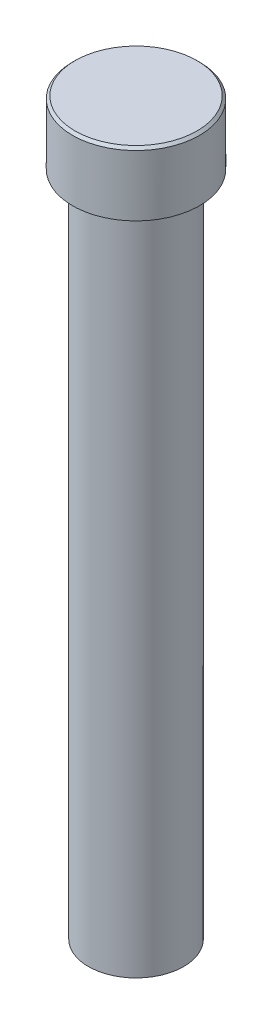
SolidWorks part; units mm, degrees
ref_plane "Front Plane" through (0, 0, 0) normal (0, 0, 1) x (1, 0, 0)
ref_plane "Top Plane" through (0, 0, 0) normal (0, 1, 0) x (1, 0, 0)
ref_plane "Right Plane" through (0, 0, 0) normal (1, 0, 0) x (0, 0, -1)
sketch "Sketch2" plane through (0, 0, 0) normal (0, 0, 1) x (1, 0, 0)
  line L0 (4.7625, 0) -> (4.7625, 66.675)
  line L1 (0, 0) -> (4.7625, 0)
  line L2 (0, 0) -> (0, 73.025)
  line L3 (0, 73.025) -> (6.35, 73.025)
  line L5 (4.7625, 66.675) -> (6.35, 66.675)
  line L6 (6.35, 73.025) -> (6.35, 66.675)
  point P5 (4.7625, 0)
  point P6 (30.2153, 51.4506)
  dimension "D1" = 73.025
  dimension "D2" = 4.7625
  dimension "D3" = 6.35
  dimension "D4" = 6.35
revolve "Revolve1" add sketch "Sketch2" angle 360 about L2
chamfer "Chamfer1" distance 0.254 angle 45 1 edges at (0, 73.025, -6.35)
